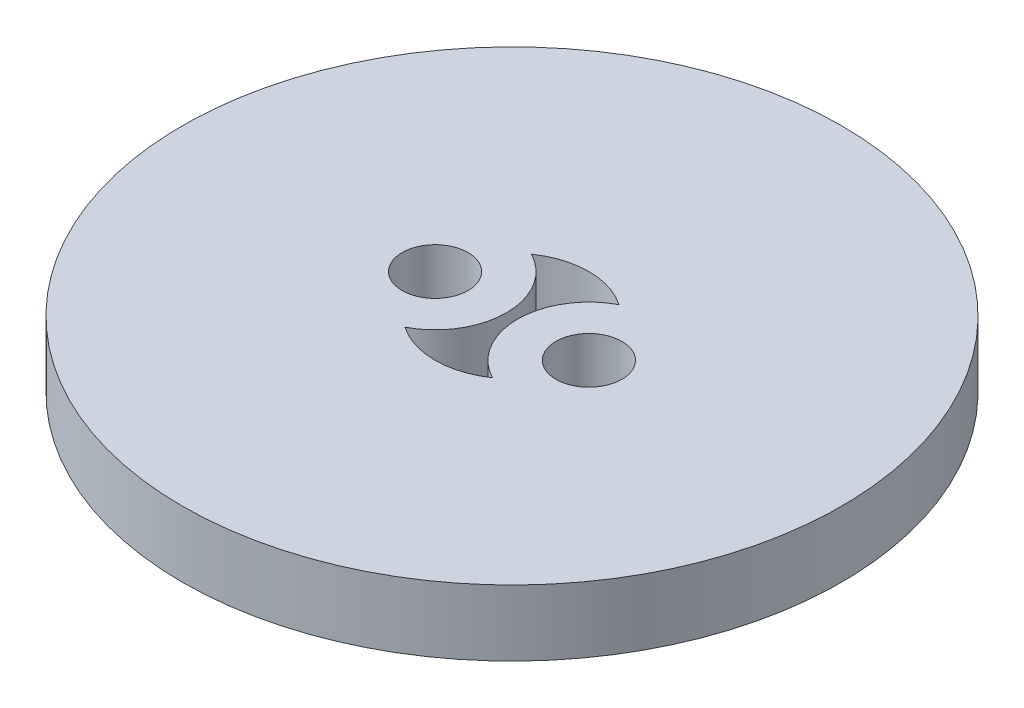
SolidWorks part; units mm, degrees
ref_plane "Plan de face" through (0, 0, 0) normal (0, 0, 1) x (1, 0, 0)
ref_plane "Plan de dessus" through (0, 0, 0) normal (0, 1, 0) x (1, 0, 0)
ref_plane "Plan de droite" through (0, 0, 0) normal (1, 0, 0) x (0, 0, -1)
sketch "Esquisse1" plane through (0, 0, 0) normal (0, 1, 0) x (1, 0, 0)
  line L0 (-3.5, 0) -> (3.5, 0) construction
  circle A0 centre (0, 0) radius 15
  circle A2 centre (-3.5, 0) radius 1.5
  circle A3 centre (3.5, 0) radius 1.5
  arc A4 (1.9911, 2.8785) -> (1.9911, -2.8785) centre (3.5, 0) ccw
  arc A5 (-1.9911, -2.8785) -> (-1.9911, 2.8785) centre (-3.5, 0) ccw
  arc A6 (-1.9911, -2.8785) -> (1.9911, -2.8785) centre (0, 0) ccw
  arc A9 (1.9911, 2.8785) -> (-1.9911, 2.8785) centre (0, 0) ccw
  circle A10 centre (-3.5, 0) radius 3.25 construction
  circle A11 centre (3.5, 0) radius 3.25 construction
  dimension "D1" = 30
  dimension "D2" = 6.5
  dimension "D3" = 6.5
  dimension "D4" = 7
  dimension "D5" = 3
  dimension "D6" = 3
  dimension "D7" = 3.5
  dimension "D8" = 3.5
  dimension "D9" = 3.25
  dimension "D10" = 3.25
  dimension "D11" = 3.5
extrude "Boss.-Extru.1" add sketch "Esquisse1" along normal blind 3
